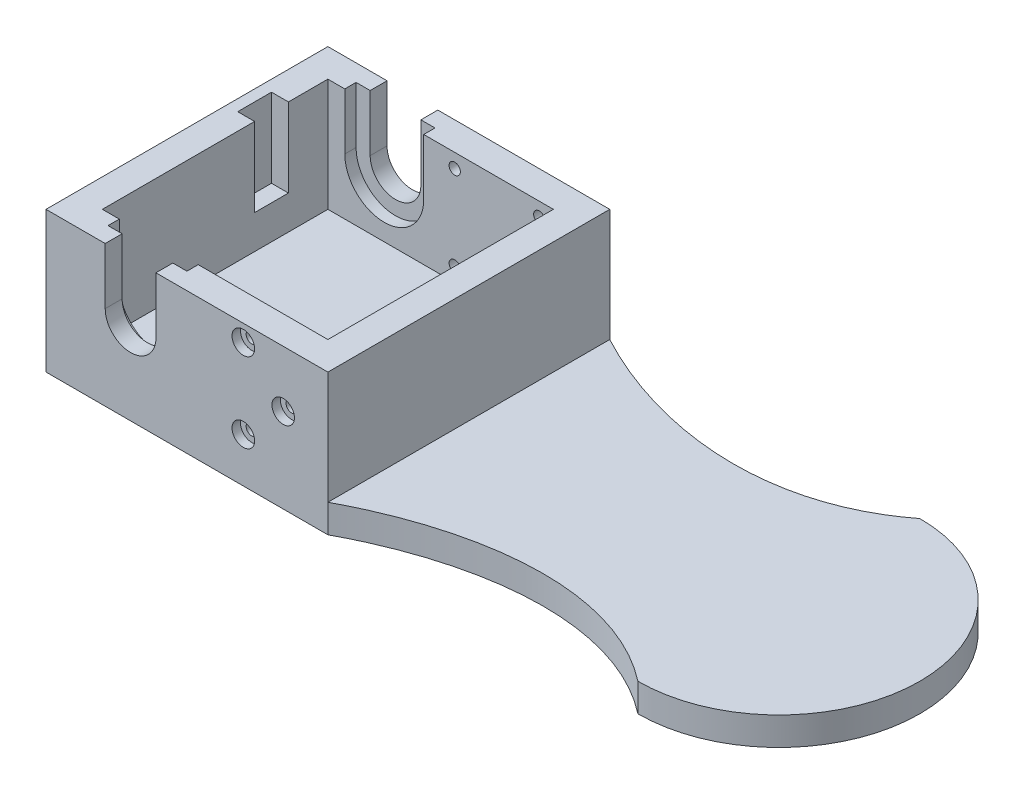
SolidWorks part; units mm, degrees
ref_plane "Alzado" through (0, 0, 0) normal (0, 0, 1) x (1, 0, 0)
ref_plane "Planta" through (0, 0, 0) normal (0, 1, 0) x (1, 0, 0)
ref_plane "Vista lateral" through (0, 0, 0) normal (1, 0, 0) x (0, 0, -1)
sketch "Croquis1" plane through (0, 0, 0) normal (0, 1, 0) x (1, 0, 0)
  line L0 (0, 0) -> (0, 40) construction
  line L1 (0, 40) -> (40, 40) construction
  line L2 (40, 40) -> (40, 0) construction
  line L3 (40, 0) -> (0, 0) construction
  line L4 (0, 0) -> (-5, 0) construction
  line L5 (-5, 0) -> (-5, 45)
  line L6 (0, 40) -> (10, 40) construction
  line L7 (10, 40) -> (10, 0) construction
  line L8 (10, 0) -> (10, 45) construction
  line L9 (10, 45) -> (-5, 45) construction
  line L10 (10, 45) -> (125, 45) construction
  line L11 (125, 45) -> (125, -5) construction
  line L12 (125, -5) -> (-5, -5) construction
  line L13 (-5, -5) -> (-5, 0) construction
  line L15 (-5, 45) -> (125, 45)
  line L16 (-5, 45) -> (-5, -5)
  line L17 (-5, -5) -> (125, -5)
  line L18 (125, 45) -> (125, -5)
extrude "Saliente-Extruir1" add sketch "Croquis1" along normal blind 25 contours L18 L15 L5 L16 L17
sketch "Croquis2" plane through (0, 25, 0) normal (0, 1, 0) x (1, 0, 0)
  line L1 (0, 0) -> (40, 0)
  line L2 (0, 0) -> (0, 40)
  line L3 (0, 40) -> (40, 40)
  line L4 (40, 0) -> (40, 40)
extrude "Cortar-Extruir1" cut sketch "Croquis2" against normal blind 20
sketch "Croquis3" plane through (0, 0, -40) normal (0, 0, 1) x (1, 0, 0)
  line L0 (0, 25) -> (0, 5) construction
  line L1 (0, 5) -> (0, 25) construction
  line L2 (0, 5) -> (0, 15) construction
  line L3 (0, 15) -> (10, 15) construction
  line L5 (14.5, 15) -> (5.5, 15)
  line L6 (14.5, 15) -> (14.5, 32.167)
  line L7 (14.5, 32.167) -> (5.5, 32.167)
  line L8 (5.5, 15) -> (5.5, 32.167)
  circle A0 centre (10, 15) radius 4.5
  line M1 (40, 25) -> (0, 25)
extrude "Cortar-Extruir2" cut sketch "Croquis3" against normal blind 20 and the other way blind 70 contours A0 L6 L8 M1 | L5 A0 | L5 A0
sketch "Croquis4" plane through (0, 0, -40) normal (0, 0, 1) x (1, 0, 0)
  line L1 (17, 15) -> (3, 15)
  line L2 (17, 15) -> (17, 33.1344)
  line L3 (17, 33.1344) -> (3, 33.1344)
  line L4 (3, 15) -> (3, 33.1344)
  circle A0 centre (10, 15) radius 7
  arc M1 (14.5, 15) -> (5.5, 15) centre (10, 15) cw
  line M2 (5.5, 15) -> (5.5, 25)
  line M3 (5.5, 25) -> (0, 25)
  line M7 (40, 25) -> (14.5, 25)
  line M8 (14.5, 25) -> (14.5, 15)
extrude "Cortar-Extruir3" cut sketch "Croquis4" against normal blind 2 and the other way blind 42 contours L1 A0 M8 | L1 A0 M1 | A0 L1 M2 | A0 L4 M2 M3 | A0 L2 M7 M8
sketch "Croquis5" plane through (0, 25, 0) normal (0, 1, 0) x (1, 0, 0)
  line L0 (40, 40) -> (40, 33) construction
  line L1 (40, 33) -> (43, 33) construction
  line L2 (43, 33) -> (43, 27) construction
  line L3 (43, 27) -> (40, 27) construction
  line L4 (40, 0) -> (40, 40) construction
  line L5 (40, 27) -> (40, 33) construction
  line L7 (40, 33) -> (43, 33)
  line L8 (40, 33) -> (40, 27)
  line L9 (40, 27) -> (43, 27)
  line L10 (43, 33) -> (43, 27)
sketch "Croquis6" plane through (0, 0, 5) normal (0, 0, 1) x (1, 0, 0)
  line L0 (-5, 0) -> (45, 0) construction
  line L1 (45, 0) -> (45, 25) construction
  line L2 (14.5, 25) -> (125, 25) construction
  line L3 (85, 5) -> (135.6948, 5)
  line L4 (135.6948, 5) -> (135.6948, 25)
  line L5 (-5, 0) -> (125, 0) construction
  line L6 (45, 0) -> (45, 5)
  line L7 (45, 5) -> (85, 5)
  line L8 (45, 5) -> (45, 25)
  line L9 (45, 25) -> (125, 25)
  line L10 (125, 25) -> (125, 14.6163)
  line L11 (125, 25) -> (125, 0) construction
  line L12 (125, 9.0417) -> (131.8585, 0)
  line L13 (131.8585, 0) -> (85, -16.2741)
  line L14 (85, -16.2741) -> (85, 0)
  line L15 (135.6948, 25) -> (125, 25)
  circle A0 centre (85, 93) radius 93
  circle A1 centre (85, 93) radius 88
  line M6 (125, 0) -> (125, 25)
  line M7 (125, 25) -> (14.5, 25)
sketch "Croquis8" plane through (0, 0, -40) normal (0, 0, 1) x (1, 0, 0)
  line L0 (10, 15) -> (40, 15) construction
  line L1 (40, 15) -> (37.5, 15) construction
  line L2 (40, 15) -> (30, 15) construction
  line L3 (37.5, 15) -> (37.5, 22.5) construction
  circle A0 centre (37.5, 22.5) radius 1
  circle A1 centre (37.5, 7.5) radius 1
  circle A2 centre (22.5, 7.5) radius 1
  circle A3 centre (22.5, 22.5) radius 1
  point P16 (30, 15)
  dimension "D1" = 4
extrude "Cortar-Extruir7" cut sketch "Croquis8" against normal blind 10
sketch "Croquis9" plane through (0, 0, 0) normal (0, 0, -1) x (-1, 0, 0)
  line L0 (-10, 15) -> (-40, 15) construction
  line L1 (-40, 15) -> (-30, 25) construction
  line L2 (-10, 15) -> (-10, 25) construction
  line L3 (-10, 25) -> (-40, 25) construction
  line L4 (-17, 25) -> (-40, 25) construction
  line L5 (-14.5, 25) -> (-125, 25) construction
  line L6 (-40, 25) -> (-40, 15) construction
  line L7 (-30, 25) -> (-30, 15) construction
  line L8 (-30, 22.0711) -> (-37.0711, 15) construction
  line L9 (-30, 7.9289) -> (-37.0711, 15) construction
  circle A0 centre (-30, 22.0711) radius 1
  circle A1 centre (-37.0711, 15) radius 1
  circle A2 centre (-30, 7.9289) radius 1
extrude "Cortar-Extruir8" cut sketch "Croquis9" against normal blind 10
sketch "Croquis10" plane through (0, 0, -45) normal (0, 0, -1) x (-1, 0, 0)
  line L0 (-22.5, 22.5) -> (-37.5, 7.5) construction
  circle A0 centre (-22.5, 22.5) radius 2
  circle A1 centre (-22.5, 7.5) radius 2
  circle A2 centre (-37.5, 7.5) radius 2
  circle A3 centre (-37.5, 22.5) radius 2
  point P3 (-30, 15)
  point P15 (-30, 15)
  dimension "D1" = 4
extrude "Cortar-Extruir9" cut sketch "Croquis10" against normal blind 1.5
sketch "Croquis11" plane through (0, 0, 5) normal (0, 0, 1) x (1, 0, 0)
  circle A0 centre (30, 22.0711) radius 2
  circle A1 centre (37.0711, 15) radius 2
  circle A2 centre (30, 7.9289) radius 2
extrude "Cortar-Extruir10" cut sketch "Croquis11" against normal blind 1.5
extrude "Cortar-Extruir11" cut sketch "Croquis6" against normal blind 70 contours L8 A1 M6 M7 | A1 L3 A0 M6 | A0 L3 M6 | A1 L8 A0 L7 | A0 L8 L7
sketch "Croquis12" plane through (0, 5, 0) normal (0, 1, 0) x (1, 0, 0)
  line L0 (125, 45) -> (45, 45) construction
  line L1 (125, 45) -> (125, -5) construction
  line L5 (125, 20) -> (100, 20) construction
  line L6 (100, 45) -> (108.2635, 57.3224)
  line L7 (108.2635, 57.3224) -> (139.962, 54.2548)
  line L8 (139.962, 54.2548) -> (155.4349, 7.8249)
  line L9 (155.4349, 7.8249) -> (132.4373, -23.5013)
  line L10 (132.4373, -23.5013) -> (92.7965, -13.0495)
  line L11 (92.7965, -13.0495) -> (100, -5)
  circle A0 centre (100, 20) radius 25
  line M2 (125, 45) -> (45, 45)
  line M4 (45, -5) -> (125, -5)
  line M5 (125, -5) -> (125, 45)
extrude "Cortar-Extruir12" cut sketch "Croquis12" against normal blind 10 contours L11 L10 L9 L8 L7 L6 M2 M5 M4 | A0 M4 M5 | A0 M5 M2
sketch "Croquis13" plane through (0, 5, 0) normal (0, 1, 0) x (1, 0, 0)
  line L2 (125, 20) -> (45, 20) construction
  line L3 (45, 45) -> (45, -5) construction
  line L4 (100, 45) -> (136.0764, 53.0278)
  line L5 (136.0764, 53.0278) -> (154.6865, 18.0572)
  line L6 (154.6865, 18.0572) -> (135.4111, -29.0588)
  line L7 (135.4111, -29.0588) -> (100, -5)
  line L8 (45, -5) -> (-2.5696, -27.4801)
  line L9 (-2.5696, -27.4801) -> (140.1501, -43.1151)
  line L10 (140.1501, -43.1151) -> (174.8278, 24.4362)
  line L11 (174.8278, 24.4362) -> (136.0764, 62.5416)
  line L12 (136.0764, 62.5416) -> (45, 45)
  arc A0 (100, -5) -> (100, 45) centre (100, 20) ccw construction
  spline S0 degree 3 poles (45, 45) (61.6318, 36.0777) (83.7364, 32.3686) (100, 45) knots 0 0 0 0 1 1 1 1
  spline S1 degree 3 poles (45, -5) (61.6318, 3.9223) (83.7364, 7.6314) (100, -5) knots 0 0 0 0 1 1 1 1
extrude "Cortar-Extruir13" cut sketch "Croquis13" against normal blind 10
sketch "Croquis14" plane through (0, 25, 0) normal (0, 1, 0) x (1, 0, 0)
  line L1 (43, 27) -> (-3, 27) construction
  line L2 (-3, 27) -> (-3, 33) construction
  line L3 (-3, 33) -> (0, 33) construction
  line L4 (0, 40) -> (0, 0) construction
  line L5 (-3, 33) -> (0, 33)
  line L6 (-3, 33) -> (-3, 27)
  line L7 (-3, 27) -> (0, 27)
  line L8 (0, 33) -> (0, 27)
extrude "Cortar-Extruir14" cut sketch "Croquis14" against normal blind 14
